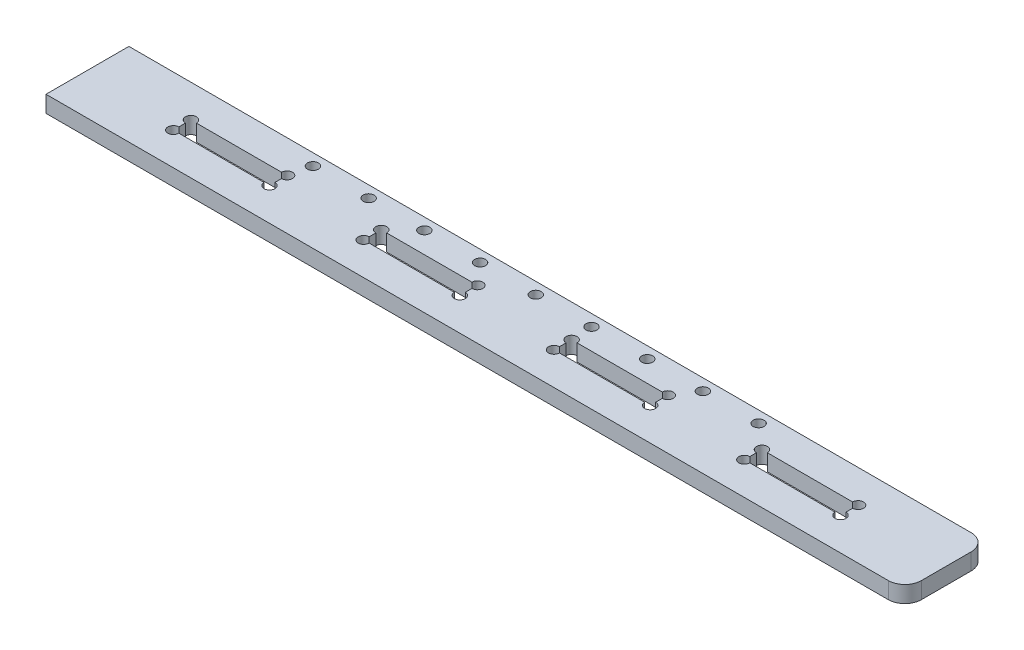
SolidWorks part; units mm, degrees
material "Acrylic (Medium-high impact)"
ref_plane "Front Plane" through (0, 0, 0) normal (0, 0, 1) x (1, 0, 0)
ref_plane "Top Plane" through (0, 0, 0) normal (0, 1, 0) x (1, 0, 0)
ref_plane "Right Plane" through (0, 0, 0) normal (1, 0, 0) x (0, 0, -1)
sketch "Sketch1" plane through (0, 0, 0) normal (0, 1, 0) x (1, 0, 0)
  line L1 (0, 0) -> (259, 0)
  line L2 (0, 0) -> (0, 25)
  line L5 (0, 25) -> (259, 25)
  line L8 (259, 25) -> (259, 0)
  dimension "D1" = 25
  dimension "D2" = 259
extrude "Boss-Extrude1" add sketch "Sketch1" along normal blind 5
sketch "Sketch4" plane through (0, 5, 0) normal (0, 1, 0) x (1, 0, 0)
  line L0 (0, 12.5) -> (259, 12.5) construction
  line L1 (0, 25) -> (0, 0) construction
  line L2 (259, 0) -> (259, 25) construction
  line L3 (28.7, 12.5) -> (28.7, 18) construction
  line L4 (0, 12.5) -> (0, 18) construction
  line L5 (0, 18) -> (28.7, 18) construction
  line L6 (28.7, 12.5) -> (28.7, 18) construction
  line L7 (28.7, 18) -> (57.4, 18) construction
  line L8 (57.4, 12.5) -> (57.4, 18) construction
  line L9 (57.4, 12.5) -> (57.4, 18) construction
  line L10 (57.4, 18) -> (86.1, 18) construction
  line L11 (86.1, 12.5) -> (86.1, 18) construction
  line L12 (86.1, 12.5) -> (86.1, 18) construction
  line L13 (86.1, 18) -> (114.8, 18) construction
  line L14 (114.8, 12.5) -> (114.8, 18) construction
  line L15 (114.8, 12.5) -> (114.8, 18) construction
  line L16 (114.8, 18) -> (143.5, 18) construction
  line L17 (143.5, 12.5) -> (143.5, 18) construction
  line L18 (143.5, 12.5) -> (143.5, 18) construction
  line L19 (143.5, 18) -> (172.2, 18) construction
  line L20 (172.2, 12.5) -> (172.2, 18) construction
  line L21 (172.2, 12.5) -> (172.2, 18) construction
  line L22 (172.2, 18) -> (200.9, 18) construction
  line L23 (200.9, 12.5) -> (200.9, 18) construction
  line L24 (200.9, 12.5) -> (200.9, 18) construction
  line L25 (200.9, 18) -> (229.6, 18) construction
  line L26 (229.6, 12.5) -> (229.6, 18) construction
  line L27 (229.6, 12.5) -> (229.6, 18) construction
  line L28 (229.6, 18) -> (258.3, 18) construction
  line L29 (258.3, 12.5) -> (258.3, 18) construction
  line L30 (43.05, 18) -> (43.05, 9.85) construction
  line L31 (100.45, 18) -> (100.45, 4.0423) construction
  line L32 (157.85, 18) -> (157.85, 6.1542) construction
  line L33 (215.25, 18) -> (215.25, 4.0423) construction
  line L34 (57.25, 15.15) -> (57.25, 9.85)
  line L35 (28.55, 15.15) -> (57.55, 15.15)
  line L36 (28.55, 15.15) -> (28.55, 9.85)
  line L37 (28.55, 9.85) -> (57.55, 9.85)
  line L38 (57.55, 15.15) -> (57.55, 9.85)
  line L39 (57.25, 15.15) -> (86.25, 15.15)
  line L40 (57.25, 9.85) -> (86.25, 9.85)
  line L41 (86.25, 15.15) -> (86.25, 9.85)
  line L42 (85.95, 15.15) -> (85.95, 9.85)
  line L43 (85.95, 15.15) -> (114.95, 15.15)
  line L44 (85.95, 9.85) -> (114.95, 9.85)
  line L45 (114.95, 15.15) -> (114.95, 9.85)
  line L46 (114.65, 15.15) -> (114.65, 9.85)
  line L47 (114.65, 15.15) -> (143.65, 15.15)
  line L48 (114.65, 9.85) -> (143.65, 9.85)
  line L49 (143.65, 15.15) -> (143.65, 9.85)
  line L50 (143.35, 15.15) -> (143.35, 9.85)
  line L51 (143.35, 15.15) -> (172.35, 15.15)
  line L52 (143.35, 9.85) -> (172.35, 9.85)
  line L53 (172.35, 15.15) -> (172.35, 9.85)
  line L54 (172.05, 15.15) -> (172.05, 9.85)
  line L55 (172.05, 15.15) -> (201.05, 15.15)
  line L56 (172.05, 9.85) -> (201.05, 9.85)
  line L57 (201.05, 15.15) -> (201.05, 9.85)
  line L58 (200.75, 15.15) -> (200.75, 9.85)
  line L59 (200.75, 15.15) -> (229.75, 15.15)
  line L60 (200.75, 9.85) -> (229.75, 9.85)
  line L61 (229.75, 15.15) -> (229.75, 9.85)
  dimension "D1" = 28.7
  dimension "D2" = 5.5
  dimension "D4" = 5.3
  dimension "D5" = 0.15
  dimension "D3" = 9
  dimension "D6" = 7
extrude "Cut-Extrude2" cut sketch "Sketch4" against normal through all
sketch "Sketch5" plane through (0, 5, 0) normal (0, 1, 0) x (1, 0, 0)
  circle A0 centre (28.55, 15.15) radius 1.65
  circle A1 centre (28.55, 9.85) radius 1.65
  circle A2 centre (57.55, 15.15) radius 1.65
  circle A3 centre (57.55, 9.85) radius 1.65
  circle A4 centre (85.95, 15.15) radius 1.65
  circle A5 centre (85.95, 9.85) radius 1.65
  circle A6 centre (114.95, 15.15) radius 1.65
  circle A7 centre (114.95, 9.85) radius 1.65
  circle A8 centre (143.35, 15.15) radius 1.65
  circle A9 centre (143.35, 9.85) radius 1.65
  circle A10 centre (172.35, 15.15) radius 1.65
  circle A11 centre (172.35, 9.85) radius 1.65
  circle A12 centre (200.75, 15.15) radius 1.65
  circle A13 centre (229.75, 15.15) radius 1.65
  circle A14 centre (229.75, 9.85) radius 1.65
  circle A15 centre (200.75, 9.85) radius 1.65
  dimension "D1" = 3.3
extrude "Cut-Extrude3" cut sketch "Sketch5" against normal through all
sketch "Sketch6" plane through (0, 0, 0) normal (0, -1, 0) x (1, 0, 0)
  line L0 (259, -21.5) -> (0, -21.5) construction
  line L1 (0, -25) -> (0, 0) construction
  line L2 (0, -12.5) -> (259, -12.5) construction
  line L3 (259, 0) -> (259, -25) construction
  line L4 (259, -25) -> (0, -25) construction
  circle A0 centre (210.2, -21.5) radius 1.65 construction
  circle A1 centre (193.4, -21.5) radius 1.65
  circle A2 centre (176.6, -21.5) radius 1.65
  circle A3 centre (159.8, -21.5) radius 1.65
  circle A4 centre (143, -21.5) radius 1.65
  circle A5 centre (126.2, -21.5) radius 1.65
  circle A6 centre (109.4, -21.5) radius 1.65
  circle A7 centre (92.6, -21.5) radius 1.65
  circle A8 centre (75.8, -21.5) radius 1.65
  circle A9 centre (59, -21.5) radius 1.65
  point P9 (259, -25)
  dimension "D3" = 3.3
  dimension "D1" = 3.5
  dimension "D2" = 48.8
  dimension "D5" = 16.8
  dimension "D4" = 10
extrude "Cut-Extrude4" cut sketch "Sketch6" against normal through all
fillet "Fillet1" radius 5 2 edges at (259, 2.5, -25) (259, 2.5, 0)
